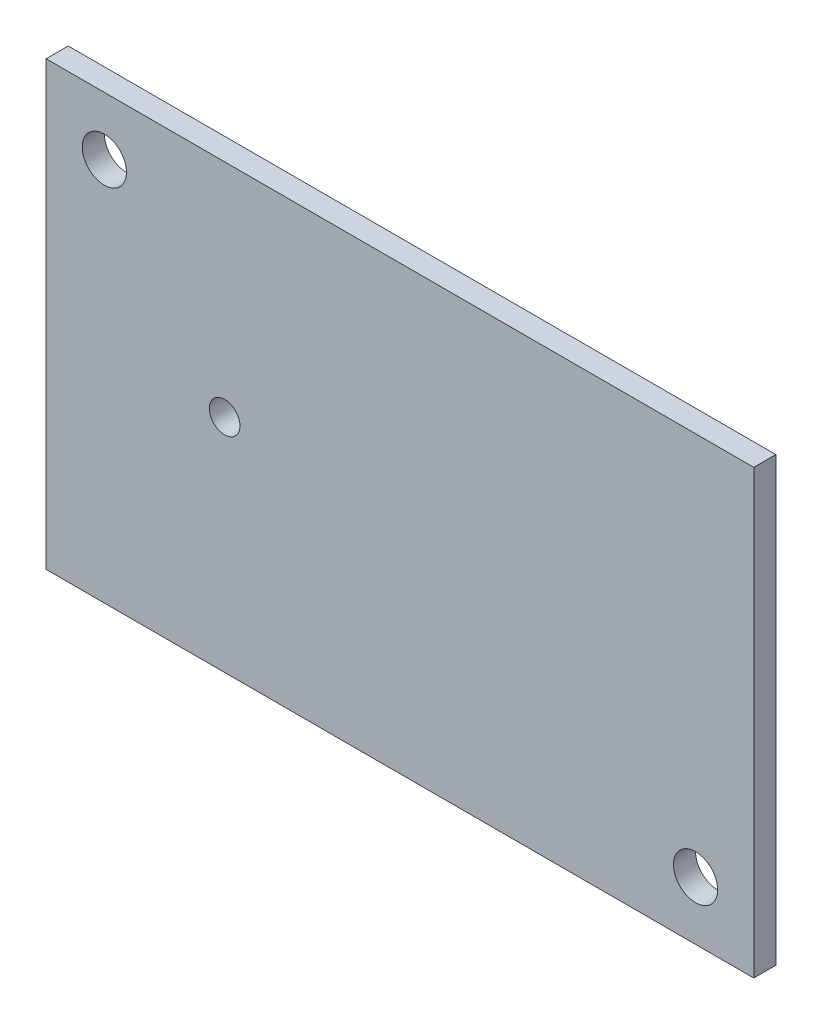
SolidWorks part; units mm, degrees
ref_plane "Front" through (0, 0, 0) normal (0, 0, 1) x (1, 0, 0)
ref_plane "Top" through (0, 0, 0) normal (0, 1, 0) x (1, 0, 0)
ref_plane "Right" through (0, 0, 0) normal (1, 0, 0) x (0, 0, -1)
sketch "Sketch1" plane through (0, 0, 0) normal (0, 0, 1) x (1, 0, 0)
  line L1 (-86.1291, 32.3273) -> (15.4709, 32.3273)
  line L2 (-86.1291, 32.3273) -> (-86.1291, -31.1727)
  line L3 (-86.1291, -31.1727) -> (15.4709, -31.1727)
  line L4 (15.4709, 32.3273) -> (15.4709, -31.1727)
  dimension "D1" = 63.5
  dimension "D2" = 101.6
extrude "Boss-Extrude1" add sketch "Sketch1" along normal blind 3.175
sketch "Sketch2" plane through (0, 0, 3.175) normal (0, 0, 1) x (1, 0, 0)
  line L0 (-86.1291, 32.3273) -> (-86.1291, -31.1727) construction
  line L1 (15.4709, 32.3273) -> (-86.1291, 32.3273) construction
  line L2 (-86.1291, -31.1727) -> (15.4709, -31.1727) construction
  line L3 (15.4709, -31.1727) -> (15.4709, 32.3273) construction
  circle A0 centre (-77.7691, 23.9673) radius 3.175
  circle A1 centre (7.1159, -22.8127) radius 3.175
  dimension "D3" = 6.35
  dimension "D4" = 6.35
  dimension "D1" = 8.36
  dimension "D2" = 8.36
  dimension "D5" = 8.36
  dimension "D6" = 8.355
extrude "Cut-Extrude1" cut sketch "Sketch2" against normal blind 3.175
sketch "Sketch3" plane through (0, 0, 3.175) normal (0, 0, 1) x (1, 0, 0)
  circle A0 centre (-60.4998, 0.5814) radius 2.2
extrude "Cut-Extrude2" cut sketch "Sketch3" against normal blind 3.175
